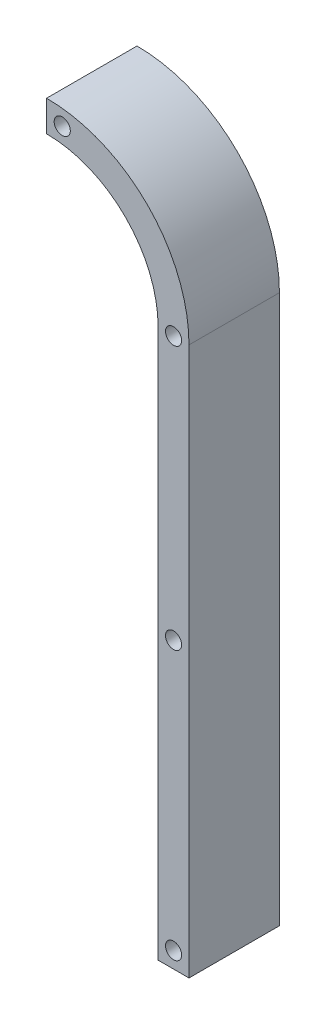
SolidWorks part; units mm, degrees
ref_plane "Front Plane" through (0, 0, 0) normal (0, 0, 1) x (1, 0, 0)
ref_plane "Top Plane" through (0, 0, 0) normal (0, 1, 0) x (1, 0, 0)
ref_plane "Right Plane" through (0, 0, 0) normal (1, 0, 0) x (0, 0, -1)
ref_plane "Plane1" through (0, 0, 0) normal (0, 0, -1) x (-1, 0, 0)
sketch "Sketch1" plane through (0, 0, 0) normal (0, 0, -1) x (-1, 0, 0)
  line L0 (149.0854, 235.6883) -> (149.0854, 242.1883)
  line L1 (119.0854, 212.1883) -> (119.0854, 96.6996)
  line L2 (119.0854, 96.6996) -> (125.5854, 96.6996)
  line L3 (125.5854, 96.6996) -> (125.5854, 212.1883)
  arc A0 (149.0854, 242.1883) -> (119.0854, 212.1883) centre (149.0854, 212.1883) ccw
  arc A1 (125.5854, 212.1883) -> (149.0854, 235.6883) centre (149.0854, 212.1883) cw
  circle A2 centre (145.7854, 238.734) radius 1.7
  circle A3 centre (122.3354, 212.1883) radius 1.7
  circle A4 centre (122.3354, 156.6996) radius 1.7
  circle A5 centre (122.3354, 100.0996) radius 1.7
extrude "Boss-Extrude1" add sketch "Sketch1" against normal blind 19.05
